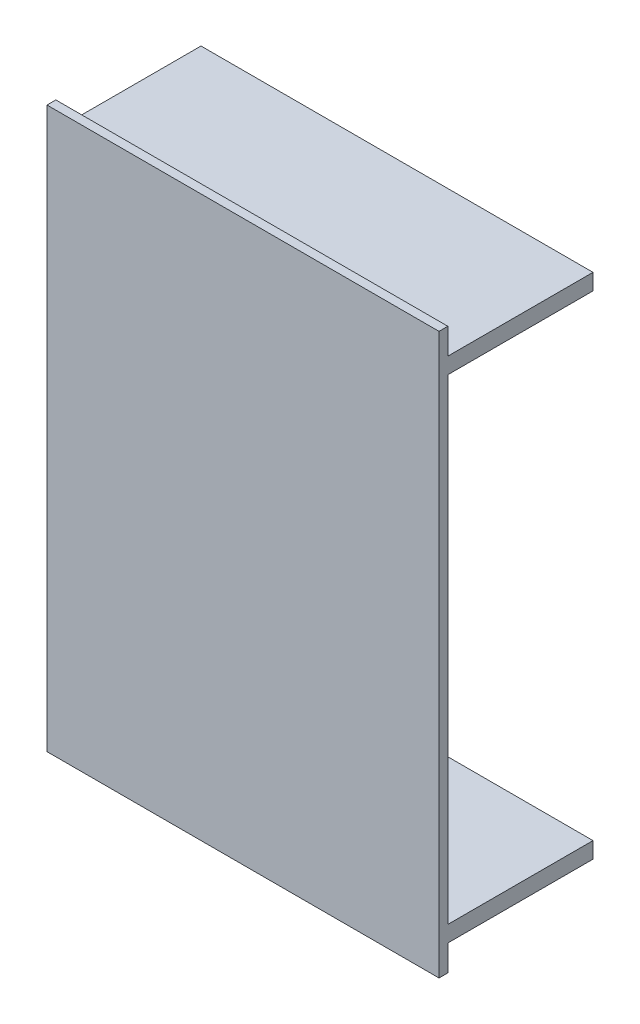
SolidWorks part; units mm, degrees
ref_plane "Front Plane" through (0, 0, 0) normal (0, 0, 1) x (1, 0, 0)
ref_plane "Top Plane" through (0, 0, 0) normal (0, 1, 0) x (1, 0, 0)
ref_plane "Right Plane" through (0, 0, 0) normal (1, 0, 0) x (0, 0, -1)
sketch "Sketch1" plane through (0, 0, 0) normal (0, 0, 1) x (1, 0, 0)
  line L1 (0, 0) -> (280, 0)
  line L2 (0, 0) -> (0, 400)
  line L3 (0, 400) -> (280, 400)
  line L4 (280, 0) -> (280, 400)
  dimension "D1" = 280
  dimension "D2" = 400
extrude "Boss-Extrude1" add sketch "Sketch1" along normal blind 6.3
sketch "Sketch4" plane through (0, 0, 0) normal (1, 0, 0) x (0, 0, -1)
  line L0 (0, 0) -> (0, 400) construction
  line L1 (0, 18.5) -> (103.7, 18.5)
  line L2 (0, 18.5) -> (0, 30)
  line L3 (0, 30) -> (103.7, 30)
  line L4 (103.7, 18.5) -> (103.7, 30)
  line L5 (-6.3, 200) -> (0, 200) construction
  line L6 (-6.3, 0) -> (-6.3, 400) construction
  line L7 (0, 370) -> (103.7, 370)
  line L8 (103.7, 381.5) -> (103.7, 370)
  line L9 (0, 381.5) -> (103.7, 381.5)
  line L10 (0, 381.5) -> (0, 370)
  dimension "D1" = 11.5
  dimension "D2" = 110
  dimension "D3" = 340
extrude "Boss-Extrude2" add sketch "Sketch4" along normal up to surface (280 mm away) up to face at (280, 200, 3.15)
ref_plane "Plane1" through (0, 0, -103.7) normal (0, 0, -1) x (-1, 0, 0)
ref_plane "Plane2" through (0, 200, 0) normal (0, 1, 0) x (1, 0, 0)
ref_plane "Plane3" through (140, 0, 0) normal (1, 0, 0) x (0, 0, -1)
ref_plane "Plane4" through (0, 0, 3.15) normal (0, 0, -1) x (-1, 0, 0)
sketch "Sketch5" plane through (0, 0, 3.15) normal (0, 0, -1) x (-1, 0, 0)
  line L0 (-140, 60.5) -> (-140, -60.5) construction
  line L1 (57.035, 200) -> (-57.035, 200) construction
  line L3 (-280, 0) -> (0, 0)
  line L4 (-280, 0) -> (-280, 400)
  line L5 (-280, 400) -> (0, 400)
  line L6 (0, 0) -> (0, 400)
  line L7 (-280, 0) -> (0, 400) construction
  line L8 (-280, 400) -> (0, 0) construction
  point P0 (-140, 200)
  point P8 (-140, 200)
